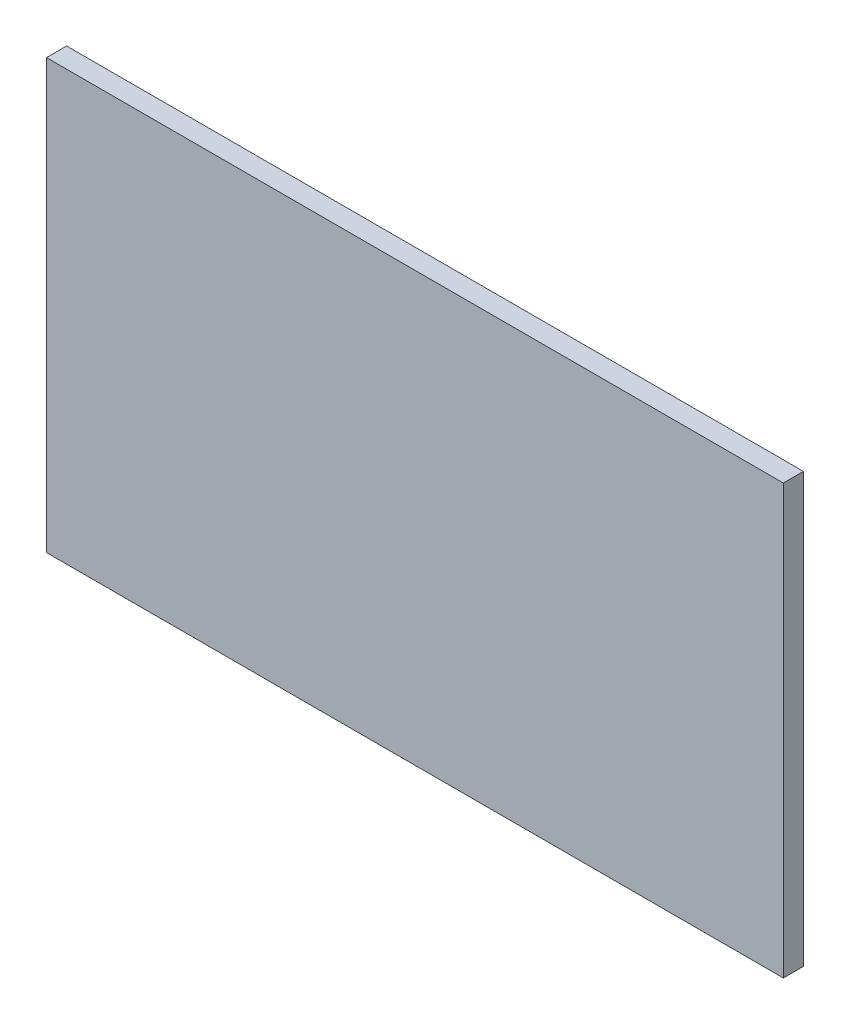
SolidWorks part; units mm, degrees
ref_plane "前视基准面" through (0, 0, 0) normal (0, 0, 1) x (1, 0, 0)
ref_plane "上视基准面" through (0, 0, 0) normal (0, 1, 0) x (1, 0, 0)
ref_plane "右视基准面" through (0, 0, 0) normal (1, 0, 0) x (0, 0, -1)
sketch "草图1" plane through (0, 0, 0) normal (0, 0, 1) x (1, 0, 0)
  line L0 (0, 0) -> (110, 0)
  line L1 (110, 0) -> (110, -64)
  line L2 (110, -64) -> (0, -64)
  line L3 (0, -64) -> (0, 0)
extrude "凸台-拉伸1" add sketch "草图1" along normal blind 3
